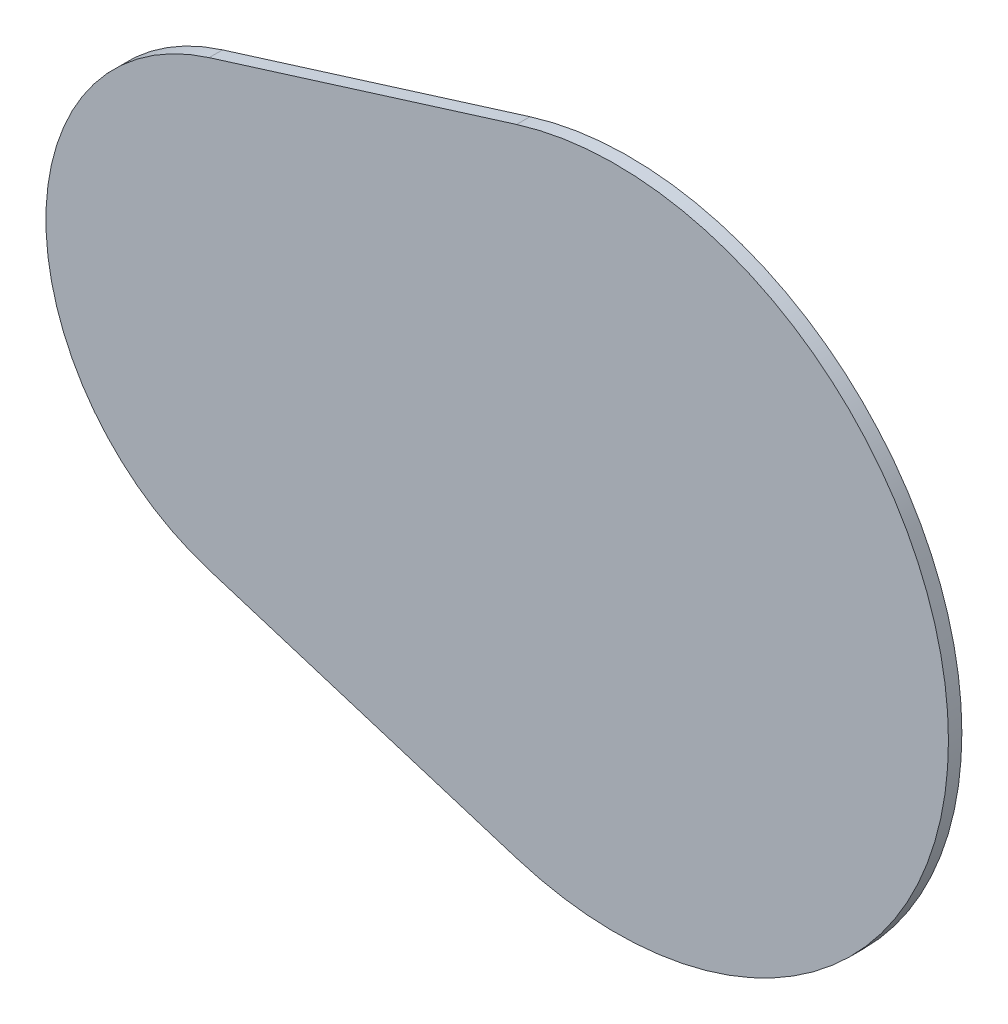
SolidWorks part; units mm, degrees
ref_plane "Front Plane" through (0, 0, 0) normal (0, 0, 1) x (1, 0, 0)
ref_plane "Top Plane" through (0, 0, 0) normal (0, 1, 0) x (1, 0, 0)
ref_plane "Right Plane" through (0, 0, 0) normal (1, 0, 0) x (0, 0, -1)
sketch "Sketch1" plane through (0, 0, 0) normal (0, 0, 1) x (1, 0, 0)
  line L0 (0, 0) -> (-279.4, 0) construction
  line L1 (-279.4, 0) -> (-12.6633, 83.1617) construction
  line L2 (-279.4, 0) -> (-12.6633, -83.1617) construction
  line L3 (-12.6633, -83.1617) -> (0, -42.545) construction
  line L4 (-12.6633, 83.1617) -> (0, 42.545) construction
  line L5 (-12.6633, 40.6167) -> (-49.0365, 29.2765) construction
  line L6 (-49.0365, -29.2765) -> (-12.6633, -40.6167) construction
  line L7 (-11.7182, -37.5856) -> (-48.0914, -26.2454)
  line L8 (-11.7182, 37.5856) -> (-48.0914, 26.2454)
  arc A2 (-48.0914, 26.2454) -> (-48.0914, -26.2454) centre (-39.9088, 0) ccw
  arc A5 (-12.6633, -40.6167) -> (-12.6633, 40.6167) centre (0, 0) ccw construction
  arc A6 (-49.0365, 29.2765) -> (-49.0365, -29.2765) centre (-39.9088, 0) ccw construction
  arc A7 (-11.7182, -37.5856) -> (-11.7182, 37.5856) centre (0, 0) ccw
  dimension "D1" = 42.545
  dimension "D2" = 3.175
  dimension "D3" = 279.4
  dimension "D4" = 42.545
  dimension "D5" = 42.545
  dimension "D6" = 38.1
extrude "Boss-Extrude1" add sketch "Sketch1" along normal blind 1.5875
equation "\"D5@Sketch1\"=\"D4@Sketch1\""
